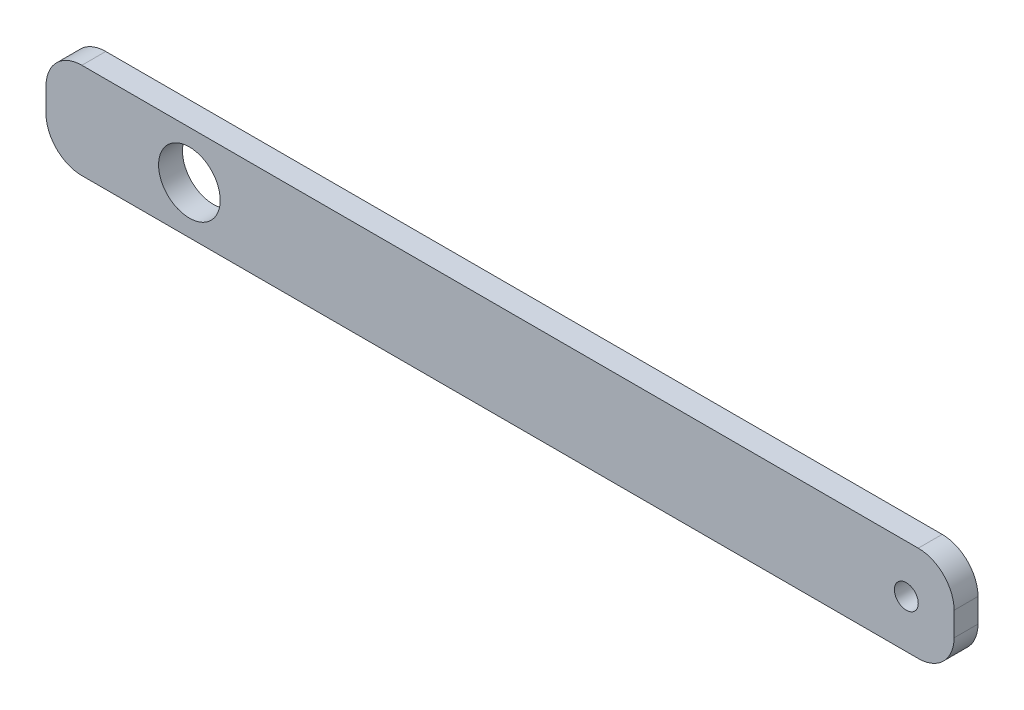
SolidWorks part; units mm, degrees
material "Teak"
ref_plane "Front Plane" through (0, 0, 0) normal (0, 0, 1) x (1, 0, 0)
ref_plane "Top Plane" through (0, 0, 0) normal (0, 1, 0) x (1, 0, 0)
ref_plane "Right Plane" through (0, 0, 0) normal (1, 0, 0) x (0, 0, -1)
sketch "Sketch1" plane through (0, 0, 0) normal (0, 0, 1) x (1, 0, 0)
  line L0 (-95, -10) -> (95, -10)
  line L1 (-95, -10) -> (-95, 10)
  line L2 (95, -10) -> (95, 10)
  line L3 (-95, 10) -> (95, 10)
  line L4 (-95, -10) -> (95, 10) construction
  line L5 (95, -10) -> (-95, 10) construction
  line L6 (-95, 0) -> (95, 0) construction
  line L7 (0, 10) -> (0, -10) construction
  circle A0 centre (-65, 0) radius 6.45
  circle A1 centre (85, 0) radius 2.5
  point P1 (0, 0)
  dimension "D3" = 12.9
  dimension "D5" = 5
  dimension "D1" = 150
  dimension "D2" = 20
  dimension "D4" = 30
  dimension "D6" = 10
extrude "Boss-Extrude1" add sketch "Sketch1" along normal blind 5
fillet "Fillet1" radius 7.5 4 edges at (-95, -10, 2.5) (-95, 10, 2.5) (95, -10, 2.5) (95, 10, 2.5)
equation "\"D1@Boss-Extrude1\"=5mm"
equation "\"p\"= 20mm"
equation "\"m\"= 1"
equation "\"hole_diam\"= 4mm"
equation "\"len_grip_1\"= 50mm"
equation "\"len_grip_2\"= 50mm"
equation "\"thick\" = 3.1mm"
equation "\"thick2\"= 20mm"
equation "\"wrist_cont_bearing_diam\"=3in"
equation "\"wrist_cont_bearing_thick\"=5/16in"
equation "\"len_forearm\"= 300mm"
equation "\"wrist_bearing_diam\"=3in"
equation "\"len_link\"= 7cm"
